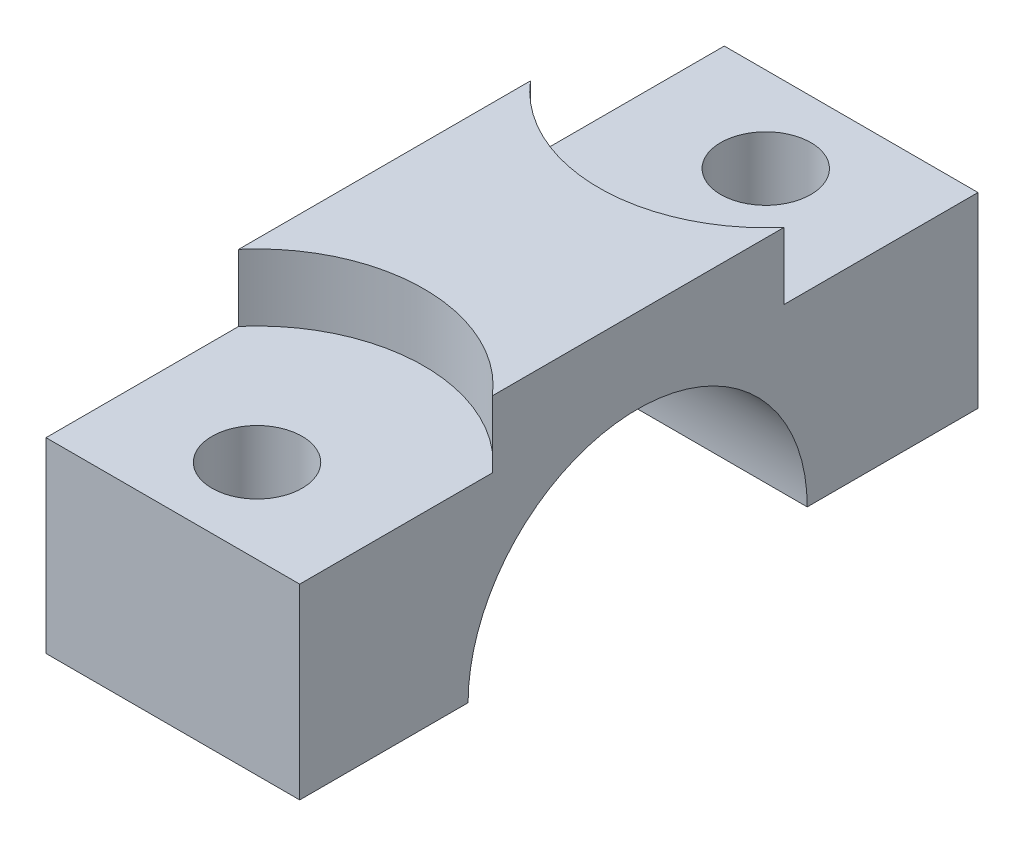
SolidWorks part; units mm, degrees
ref_plane "Front Plane" through (0, 0, 0) normal (0, 0, 1) x (1, 0, 0)
ref_plane "Top Plane" through (0, 0, 0) normal (0, 1, 0) x (1, 0, 0)
ref_plane "Right Plane" through (0, 0, 0) normal (1, 0, 0) x (0, 0, -1)
sketch "Sketch1" plane through (0, 0, 0) normal (1, 0, 0) x (0, 0, -1)
  line L1 (-25.3106, 0) -> (25.4894, 0)
  line L2 (-25.3106, 0) -> (-25.3106, 19)
  line L3 (-25.3106, 19) -> (25.4894, 19)
  line L4 (25.4894, 0) -> (25.4894, 19)
  circle A0 centre (0, 0) radius 12.7
  point P7 (0, 0)
  dimension "D3" = 25.4
  dimension "D1" = 50.8
  dimension "D2" = 19
extrude "Boss-Extrude1" add sketch "Sketch1" along normal blind 19 contours A0 L1 L4 L3 L2
sketch "Sketch2" plane through (0, 0, 0) normal (0, -1, 0) x (1, 0, 0)
  line L0 (9.5, 25.3106) -> (9.5, 12.7) construction
  line L1 (19, 25.3106) -> (0, 25.3106) construction
  line L2 (19, 12.7) -> (0, 12.7) construction
  line L3 (9.5, -12.7) -> (9.5, -25.4894) construction
  line L4 (19, -12.7) -> (0, -12.7) construction
  line L5 (19, -25.4894) -> (0, -25.4894) construction
  point P12 (9.5, 19.0053)
  point P13 (9.5, -19.0947)
hole_wizard "CBORE for M12 Hex Head Cap Screw4" positions "Sketch8" profile "Sketch9" counterbore size "M12" standard "ISO" end condition through all
sketch "Sketch8" plane through (0, 19, 0) normal (0, 1, 0) x (1, 0, 0)
  point P0 (9.5, 19.0947)
  point P3 (9.5, -19.0053)
sketch "Sketch9" plane through (9.5, 19, -19.0947) normal (1, 0, 0) x (0, 0, 1)
  line L0 (0, 0) -> (0, 19)
  line L1 (0, 19) -> (3.375, 19)
  line L3 (3.375, 19) -> (3.375, 5)
  line L4 (3.375, 5) -> (12.5, 5)
  line L5 (12.5, 5) -> (12.5, 0)
  line L7 (12.5, 0) -> (0, 0)
  line L11 (0, -6.35) -> (0, 107.95) construction
  dimension "Thru Hole Dia." = 6.75
  dimension "Thru Hole Depth" = 19
  dimension "C'Bore Dia." = 25
  dimension "C'Bore Depth" = 5
